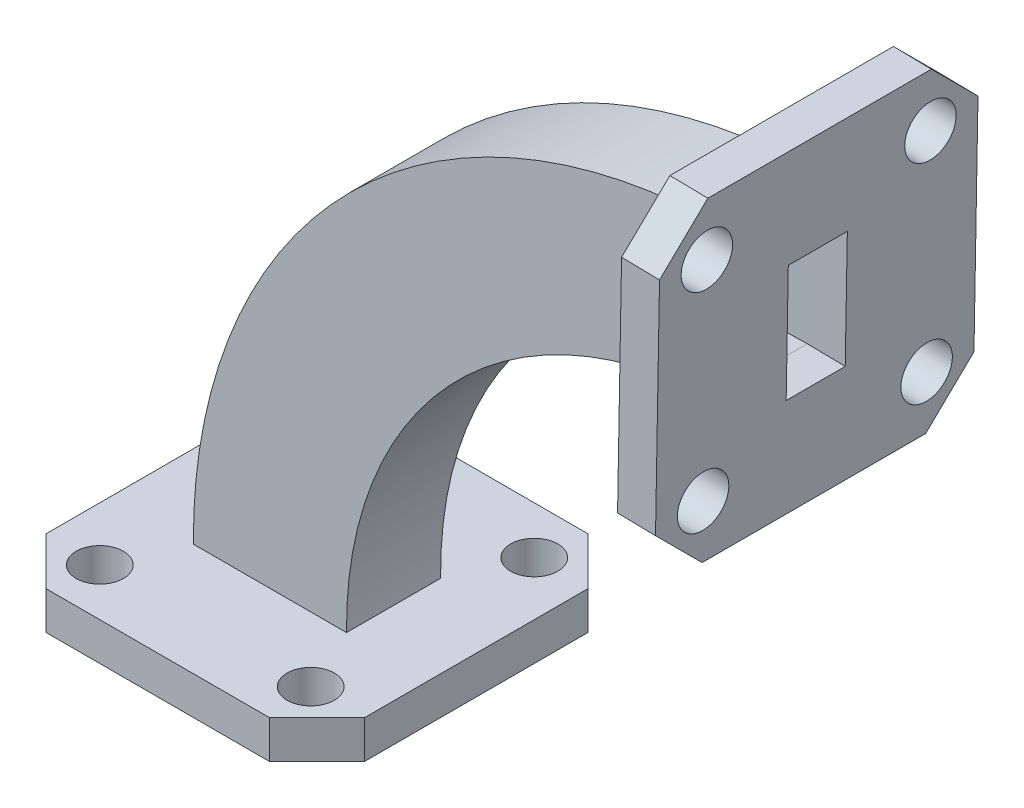
SolidWorks part; units mm, degrees
ref_plane "Front Plane" through (0, 0, 0) normal (0, 0, 1) x (1, 0, 0)
ref_plane "Top Plane" through (0, 0, 0) normal (0, 1, 0) x (1, 0, 0)
ref_plane "Right Plane" through (0, 0, 0) normal (1, 0, 0) x (0, 0, -1)
sketch "Sketch1" plane through (0, 0, 0) normal (0, 1, 0) x (1, 0, 0)
  line L0 (0, 19.4902) -> (0, -21.8512) construction
  line L1 (-9.5885, -9.5885) -> (9.5885, -9.5885)
  line L2 (-9.5885, -9.5885) -> (-9.5885, 9.5885)
  line L3 (-9.5885, 9.5885) -> (9.5885, 9.5885)
  line L4 (9.5885, -9.5885) -> (9.5885, 9.5885)
  line L5 (-17.9724, 0) -> (27.4645, 0) construction
  dimension "D1" = 19.177
  dimension "D2" = 19.177
extrude "Boss-Extrude1" add sketch "Sketch1" along normal blind 2.286
sketch "Sketch2" plane through (0, 2.286, 0) normal (0, 1, 0) x (1, 0, 0)
  line L0 (0, 5.8921) -> (0, -8.8558) construction
  line L1 (-3.556, -1.778) -> (3.556, -1.778)
  line L2 (-3.556, -1.778) -> (-3.556, 1.778)
  line L3 (-3.556, 1.778) -> (3.556, 1.778)
  line L4 (3.556, -1.778) -> (3.556, 1.778)
  line L7 (-6.5625, 0) -> (7.9456, 0) construction
  circle A0 centre (-6.35, 6.731) radius 1.4224
  circle A1 centre (6.35, 6.731) radius 1.4224
  circle A2 centre (6.35, -6.731) radius 1.4224
  circle A3 centre (-6.35, -6.731) radius 1.4224
  dimension "D3" = 2.8448
  dimension "D1" = 3.556
  dimension "D2" = 7.112
  dimension "D4" = 6.35
  dimension "D5" = 6.731
  dimension "D6" = 6.35
  dimension "D7" = 6.731
extrude "Cut-Extrude1" cut sketch "Sketch2" against normal blind 2.286
sketch "Sketch3" plane through (0, 2.286, 0) normal (0, 1, 0) x (1, 0, 0)
  line L0 (0, 6.3014) -> (0, -6.7671) construction
  line L1 (-4.6101, -2.8321) -> (4.6101, -2.8321)
  line L2 (-4.6101, -2.8321) -> (-4.6101, 2.8321)
  line L3 (-4.6101, 2.8321) -> (4.6101, 2.8321)
  line L4 (4.6101, -2.8321) -> (4.6101, 2.8321)
  line L5 (-7.6774, 0) -> (7.3528, 0) construction
  line L6 (3.556, 1.778) -> (-3.556, 1.778) construction
  line L7 (-3.556, 1.778) -> (-3.556, -1.778) construction
  line L8 (-3.556, -1.778) -> (3.556, -1.778) construction
  line L9 (3.556, -1.778) -> (3.556, 1.778) construction
  line L10 (3.556, 1.778) -> (-3.556, 1.778)
  line L11 (-3.556, 1.778) -> (-3.556, -1.778)
  line L12 (-3.556, -1.778) -> (3.556, -1.778)
  line L13 (3.556, -1.778) -> (3.556, 1.778)
  dimension "D1" = 1.0541
  dimension "D2" = 1.0541
sketch "Sketch4" plane through (0, 0, 0) normal (0, 0, 1) x (1, 0, 0)
  line L0 (-7.6774, 2.286) -> (7.3528, 2.286) construction
  line L1 (-4.6101, 2.286) -> (4.6101, 2.286) construction
  arc A0 (4.6101, 2.286) -> (27.7241, 25.5583) centre (27.5957, 2.5713) cw
  dimension "D3" = 22.9874
  dimension "D1" = 22.987
  dimension "D2" = 23.114
sweep "Sweep1" add profiles "Sketch3" path "Sketch4"
sketch "Sketch5" plane through (27.2553, -0.4906, 0) normal (0.9998, -0.018, 0) x (0, 0, -1)
  line L0 (0, 35.2733) -> (0, 26.0531) construction
  line L1 (-9.5885, 21.0747) -> (9.5885, 21.0747)
  line L2 (-9.5885, 21.0747) -> (-9.5885, 40.2517)
  line L3 (-9.5885, 40.2517) -> (9.5885, 40.2517)
  line L4 (9.5885, 21.0747) -> (9.5885, 40.2517)
  line L5 (2.8321, 35.2733) -> (-2.8321, 35.2733) construction
  line L6 (-2.8321, 26.0531) -> (2.8321, 26.0531) construction
  line L7 (-2.8321, 30.6632) -> (2.8321, 30.6632) construction
  line L8 (-2.8321, 35.2733) -> (-2.8321, 26.0531) construction
  line L9 (2.8321, 26.0531) -> (2.8321, 35.2733) construction
  line L11 (-1.778, 34.2192) -> (1.778, 34.2192)
  line L12 (-1.778, 34.2192) -> (-1.778, 27.1072)
  line L13 (-1.778, 27.1072) -> (1.778, 27.1072)
  line L14 (1.778, 34.2192) -> (1.778, 27.1072)
  circle A0 centre (-6.731, 37.0132) radius 1.5494
  circle A1 centre (6.731, 37.0132) radius 1.5494
  circle A2 centre (-6.731, 24.3132) radius 1.5494
  circle A3 centre (6.731, 24.3132) radius 1.5494
  dimension "D7" = 3.0988
  dimension "D1" = 19.177
  dimension "D2" = 19.177
  dimension "D3" = 6.35
  dimension "D4" = 6.731
  dimension "D5" = 6.731
  dimension "D6" = 6.35
extrude "Boss-Extrude2" add sketch "Sketch5" along normal blind 2.286
chamfer "Chamfer1" distance 2.8575 angle 45 8 edges at (-9.5885, 1.143, 9.5885) (9.5885, 1.143, 9.5885) (9.5885, 1.143, -9.5885) (-9.5885, 1.143, -9.5885) (29.1224, 39.734, -9.5885) (29.1224, 39.734, 9.5885) (28.7773, 20.5601, -9.5885) (28.7773, 20.5601, 9.5885)
